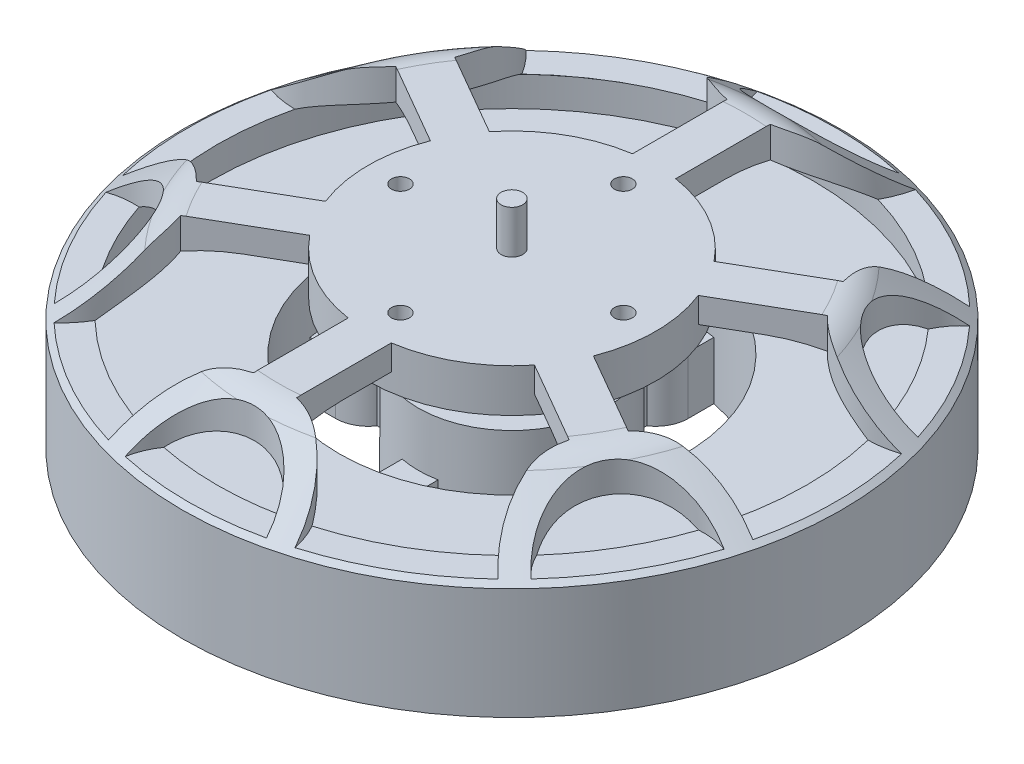
SolidWorks part; units mm, degrees
ref_plane "Front Plane" through (0, 0, 0) normal (0, 0, 1) x (1, 0, 0)
ref_plane "Top Plane" through (0, 0, 0) normal (0, 1, 0) x (1, 0, 0)
ref_plane "Right Plane" through (0, 0, 0) normal (1, 0, 0) x (0, 0, -1)
ref_axis "Axis1" through (0, 40.089, 0) along (0, -1, 0)
sketch "Sketch1" plane through (0, 0, 0) normal (0, 0, 1) x (1, 0, 0)
  line L0 (0, 0) -> (9.65, 0)
  line L1 (9.65, 0) -> (9.65, 3.93)
  line L2 (9.65, 3.93) -> (27.5, 3.93)
  line L3 (27.5, 3.93) -> (45.83, 8.08)
  line L4 (45.83, 8.08) -> (45.83, 23.58)
  line L5 (45.83, 23.58) -> (36.1322, 30.9557)
  line L6 (32.5, 32.18) -> (1.5, 32.18)
  line L7 (1.5, 32.18) -> (1.5, 38.18)
  line L8 (1.5, 38.18) -> (0, 38.18)
  line L9 (0, 38.18) -> (0, 0) construction
  line L10 (0, 0) -> (0, 38.18)
  arc A0 (36.1322, 30.9557) -> (32.5, 32.18) centre (32.5, 26.18) ccw
  dimension "D10" = 6
  dimension "D1" = 3
  dimension "D2" = 6
  dimension "D3" = 28.25
  dimension "D4" = 3.93
  dimension "D5" = 19.3
  dimension "D6" = 4.15
  dimension "D7" = 91.66
  dimension "D8" = 55
  dimension "D9" = 65
  dimension "D11" = 15.5
revolve "Revolve1" add sketch "Sketch1" angle 360 about L9
sketch "Sketch2" plane through (0, 3.93, 0) normal (0, -1, 0) x (1, 0, 0)
  line L0 (0, 0) -> (0, 27.5) construction
  line L1 (2.5, 12.7574) -> (2.5, 16.2583)
  line L2 (4.5, 20) -> (4.5, 23.5744)
  line L3 (0, 0) -> (16.9706, 16.9706) construction
  line L4 (20, 4.5) -> (23.5744, 4.5)
  line L5 (12.7574, 2.5) -> (16.2583, 2.5)
  line L6 (20, -4.5) -> (23.5744, -4.5)
  line L7 (4.5, -20) -> (4.5, -23.5744)
  line L8 (2.5, -12.7574) -> (2.5, -16.2583)
  line L9 (12.7574, -2.5) -> (16.2583, -2.5)
  line L10 (-4.5, -20) -> (-4.5, -23.5744)
  line L11 (-20, -4.5) -> (-23.5744, -4.5)
  line L12 (-12.7574, -2.5) -> (-16.2583, -2.5)
  line L13 (-2.5, -12.7574) -> (-2.5, -16.2583)
  line L14 (-20, 4.5) -> (-23.5744, 4.5)
  line L15 (-4.5, 20) -> (-4.5, 23.5744)
  line L16 (-2.5, 12.7574) -> (-2.5, 16.2583)
  line L17 (-12.7574, 2.5) -> (-16.2583, 2.5)
  arc A0 (4.5, 23.5744) -> (23.5744, 4.5) centre (0, 0) cw
  arc A1 (4.5, 20) -> (2.5, 16.2583) centre (0, 20) cw
  arc A2 (2.5, 12.7574) -> (12.7574, 2.5) centre (0, 0) cw
  circle A3 centre (0, 0) radius 27.5 construction
  arc A4 (20, 4.5) -> (16.2583, 2.5) centre (20, 0) ccw
  arc A5 (20, -4.5) -> (16.2583, -2.5) centre (20, 0) cw
  arc A6 (23.5744, -4.5) -> (4.5, -23.5744) centre (0, 0) cw
  arc A7 (4.5, -20) -> (2.5, -16.2583) centre (0, -20) ccw
  arc A8 (12.7574, -2.5) -> (2.5, -12.7574) centre (0, 0) cw
  arc A9 (-4.5, -20) -> (-2.5, -16.2583) centre (0, -20) cw
  arc A10 (-4.5, -23.5744) -> (-23.5744, -4.5) centre (0, 0) cw
  arc A11 (-20, -4.5) -> (-16.2583, -2.5) centre (-20, 0) ccw
  arc A12 (-2.5, -12.7574) -> (-12.7574, -2.5) centre (0, 0) cw
  arc A13 (-20, 4.5) -> (-16.2583, 2.5) centre (-20, 0) cw
  arc A14 (-23.5744, 4.5) -> (-4.5, 23.5744) centre (0, 0) cw
  arc A15 (-4.5, 20) -> (-2.5, 16.2583) centre (0, 20) ccw
  arc A16 (-12.7574, 2.5) -> (-2.5, 12.7574) centre (0, 0) cw
  point P4 (0, 20)
  point P51 (0, 0)
  dimension "D2" = 13
  dimension "D5" = 24
  dimension "D1" = 20
  dimension "D3" = 5
  dimension "D4" = 9
  dimension "D6" = 45
  dimension "D7" = 4
hole_wizard "M4x0.7 Tapped Hole1" positions "3DSketch1" profile "Sketch4" tap size "M4x0.7" standard "ANSI Metric"
sketch3d "3DSketch1"
  point P0 (-20, 3.93, 0)
  point P3 (0, 3.93, 20)
  point P6 (20, 3.93, 0)
  point P9 (0, 3.93, -20)
sketch "Sketch4" plane through (-20, 3.93, 0) normal (1, 0, 0) x (0, 0, -1)
  line L0 (0, 0) -> (0, 8.9914)
  line L1 (0, 8.9914) -> (1.65, 8)
  line L2 (1.65, 8) -> (1.65, 0)
  line L5 (1.65, 0) -> (0, 0)
  line L10 (0, 8.9914) -> (-1.65, 8) construction
  line L11 (0, -6.35) -> (0, 107.95) construction
  dimension "Tap Drill Dia." = 3.3
  dimension "Tap Drill Depth" = 8
  dimension "Drill Angle" = 118
cosmetic thread "Hole Thread1" parameters "D1"=7.874, "D2"=4
cosmetic thread "Hole Thread2" parameters "D1"=7.874, "D2"=4
cosmetic thread "Hole Thread3" parameters "D1"=7.874, "D2"=4
cosmetic thread "Hole Thread4" parameters "D1"=7.874, "D2"=4
extrude "Cut-Extrude1" cut sketch "Sketch2" against normal blind 8
sketch "Sketch5" plane through (0, 0, 0) normal (0, 0, 1) x (1, 0, 0)
  line L0 (24, 19.43) -> (41.83, 19.43)
  line L1 (-27.5, 3.93) -> (27.5, 3.93) construction
  line L2 (41.83, 19.43) -> (41.83, 23.58)
  line L3 (45.83, 8.08) -> (45.83, 23.58) construction
  line L4 (10, 19.43) -> (13, 19.43)
  line L5 (13, 19.43) -> (13, 11.93)
  line L6 (13, 11.93) -> (24, 11.93)
  line L7 (24, 11.93) -> (24, 19.43)
  line L8 (0, 40.089) -> (0, -1.909) construction
  line L9 (4.5, 11.93) -> (23.5744, 11.93) construction
  line L10 (45.83, 23.58) -> (-45.83, 23.58) construction
  line L11 (20, 28.68) -> (26.6996, 28.68)
  line L12 (32.5, 32.18) -> (-32.5, 32.18) construction
  line L13 (41.83, 23.58) -> (45.83, 20.5378) construction
  line L14 (45.83, 23.58) -> (36.1322, 30.9557) construction
  line L15 (20, 28.68) -> (20, 26.18)
  line L16 (20, 26.18) -> (10, 26.18)
  line L17 (10, 26.18) -> (10, 19.43)
  arc A0 (26.6996, 28.68) -> (41.83, 23.58) centre (26.6996, 3.6861) cw
  dimension "D1" = 15.5
  dimension "D2" = 4
  dimension "D3" = 13
  dimension "D4" = 24
  dimension "D5" = 3.5
  dimension "D6" = 20
  dimension "D7" = 6
  dimension "D8" = 10
revolve "Cut-Revolve3" cut sketch "Sketch5" angle 360 about axis through (0, 40.089, 0) along (0, -1, 0)
sketch "Sketch6" plane through (0, 0, 0) normal (0, 1, 0) x (1, 0, 0)
  line L0 (-3, 19.7737) -> (-3, 32.9241)
  line L1 (3, 19.7737) -> (3, 32.9241)
  line L2 (-3, 19.7737) -> (3, 19.7737) construction
  line L3 (0, 45.83) -> (0, 35.83) construction
  line L4 (15.6245, 12.4849) -> (27.0131, 19.0601)
  line L5 (18.6245, 7.2888) -> (30.0131, 13.864)
  line L6 (15.6245, 12.4849) -> (18.6245, 7.2888) construction
  line L7 (39.6899, 22.915) -> (31.0297, 17.915) construction
  line L8 (18.6245, -7.2888) -> (30.0131, -13.864)
  line L9 (15.6245, -12.4849) -> (27.0131, -19.0601)
  line L10 (18.6245, -7.2888) -> (15.6245, -12.4849) construction
  line L11 (39.6899, -22.915) -> (31.0297, -17.915) construction
  line L12 (3, -19.7737) -> (3, -32.9241)
  line L13 (-3, -19.7737) -> (-3, -32.9241)
  line L14 (3, -19.7737) -> (-3, -19.7737) construction
  line L15 (0, -45.83) -> (0, -35.83) construction
  line L16 (-15.6245, -12.4849) -> (-27.0131, -19.0601)
  line L17 (-18.6245, -7.2888) -> (-30.0131, -13.864)
  line L18 (-15.6245, -12.4849) -> (-18.6245, -7.2888) construction
  line L19 (-39.6899, -22.915) -> (-31.0297, -17.915) construction
  line L20 (-18.6245, 7.2888) -> (-30.0131, 13.864)
  line L21 (-15.6245, 12.4849) -> (-27.0131, 19.0601)
  line L22 (-18.6245, 7.2888) -> (-15.6245, 12.4849) construction
  line L23 (-39.6899, 22.915) -> (-31.0297, 17.915) construction
  line L24 (0, 15.5) -> (15.5, 0) construction
  line L25 (15.5, 0) -> (0, -15.5) construction
  line L26 (0, -15.5) -> (-15.5, 0) construction
  line L27 (-15.5, 0) -> (0, 15.5) construction
  arc A1 (-9.9403, 44.739) -> (9.9403, 44.739) centre (0, 45.83) ccw
  circle A2 centre (0, 0) radius 45.83 construction
  arc A3 (-13.1108, 43.9146) -> (-3, 32.9241) centre (0, 45.83) ccw
  arc A4 (13.1108, 43.9146) -> (3, 32.9241) centre (0, 45.83) cw
  arc A5 (-13.1108, 43.9146) -> (-9.9403, 44.739) centre (0, 0) cw
  arc A6 (9.9403, 44.739) -> (13.1108, 43.9146) centre (0, 0) cw
  arc A7 (33.775, 30.9781) -> (43.7153, 13.7609) centre (39.6899, 22.915) ccw
  arc A8 (31.4758, 33.3116) -> (27.0131, 19.0601) centre (39.6899, 22.915) ccw
  arc A9 (44.5866, 10.603) -> (30.0131, 13.864) centre (39.6899, 22.915) cw
  arc A10 (31.4758, 33.3116) -> (33.775, 30.9781) centre (0, 0) cw
  arc A11 (43.7153, 13.7609) -> (44.5866, 10.603) centre (0, 0) cw
  arc A12 (43.7153, -13.7609) -> (33.775, -30.9781) centre (39.6899, -22.915) ccw
  arc A13 (44.5866, -10.603) -> (30.0131, -13.864) centre (39.6899, -22.915) ccw
  arc A14 (31.4758, -33.3116) -> (27.0131, -19.0601) centre (39.6899, -22.915) cw
  arc A15 (44.5866, -10.603) -> (43.7153, -13.7609) centre (0, 0) cw
  arc A16 (33.775, -30.9781) -> (31.4758, -33.3116) centre (0, 0) cw
  arc A17 (9.9403, -44.739) -> (-9.9403, -44.739) centre (0, -45.83) ccw
  arc A18 (13.1108, -43.9146) -> (3, -32.9241) centre (0, -45.83) ccw
  arc A19 (-13.1108, -43.9146) -> (-3, -32.9241) centre (0, -45.83) cw
  arc A20 (13.1108, -43.9146) -> (9.9403, -44.739) centre (0, 0) cw
  arc A21 (-9.9403, -44.739) -> (-13.1108, -43.9146) centre (0, 0) cw
  arc A22 (-33.775, -30.9781) -> (-43.7153, -13.7609) centre (-39.6899, -22.915) ccw
  arc A23 (-31.4758, -33.3116) -> (-27.0131, -19.0601) centre (-39.6899, -22.915) ccw
  arc A24 (-44.5866, -10.603) -> (-30.0131, -13.864) centre (-39.6899, -22.915) cw
  arc A25 (-31.4758, -33.3116) -> (-33.775, -30.9781) centre (0, 0) cw
  arc A26 (-43.7153, -13.7609) -> (-44.5866, -10.603) centre (0, 0) cw
  arc A27 (-43.7153, 13.7609) -> (-33.775, 30.9781) centre (-39.6899, 22.915) ccw
  arc A28 (-44.5866, 10.603) -> (-30.0131, 13.864) centre (-39.6899, 22.915) ccw
  arc A29 (-31.4758, 33.3116) -> (-27.0131, 19.0601) centre (-39.6899, 22.915) cw
  arc A30 (-44.5866, 10.603) -> (-43.7153, 13.7609) centre (0, 0) cw
  arc A31 (-33.775, 30.9781) -> (-31.4758, 33.3116) centre (0, 0) cw
  arc A32 (3, 19.7737) -> (15.6245, 12.4849) centre (0, 0) cw
  arc A33 (18.6245, 7.2888) -> (18.6245, -7.2888) centre (0, 0) cw
  arc A34 (15.6245, -12.4849) -> (3, -19.7737) centre (0, 0) cw
  arc A35 (-3, -19.7737) -> (-15.6245, -12.4849) centre (0, 0) cw
  arc A36 (-18.6245, -7.2888) -> (-18.6245, 7.2888) centre (0, 0) cw
  arc A37 (-3, 19.7737) -> (-15.6245, 12.4849) centre (0, 0) ccw
  point P0 (0, 19.7737)
  point P17 (0, 15.5)
  point P28 (15.5, 0)
  point P38 (0, -15.5)
  point P68 (0, 0)
  point P69 (-15.5, 0)
  dimension "D1" = 6
  dimension "D3" = 3.25
  dimension "D5" = 20
  dimension "D2" = 6
  dimension "D4" = 10
  dimension "D6" = 15.5
extrude "Cut-Extrude3" cut sketch "Sketch6" against normal blind 8 from surface at 32.18 flip side to cut starting at face at (0, 32.18, 1.5)
hole_wizard "M3x0.5 Tapped Hole1" positions "Sketch8" profile "Sketch10" tap size "M3x0.5" standard "ANSI Metric" end condition up to next
sketch "Sketch8" plane through (0, 32.18, 0) normal (0, 1, 0) x (1, 0, 0)
  point P0 (0, 15.5)
  point P3 (15.5, 0)
  point P6 (0, -15.5)
  point P9 (-15.5, 0)
sketch "Sketch10" plane through (0, 32.18, -15.5) normal (1, 0, 0) x (0, 0, 1)
  line L0 (0, 0) -> (0, 6)
  line L1 (0, 6) -> (1.25, 6)
  line L2 (1.25, 6) -> (1.25, 0)
  line L5 (1.25, 0) -> (0, 0)
  line L11 (0, -6.35) -> (0, 107.95) construction
  dimension "Thru Tap Drill Dia." = 2.5
  dimension "Thru Tap Drill Depth" = 6
cosmetic thread "Hole Thread5" parameters "D2"=3
cosmetic thread "Hole Thread6" parameters "D2"=3
cosmetic thread "Hole Thread7" parameters "D2"=3
cosmetic thread "Hole Thread8" parameters "D2"=3
sketch "Sketch11" plane through (0, 0, 0) normal (0, 1, 0) x (1, 0, 0)
  line L0 (-26.0427, 21.4465) -> (-21.4465, 26.0427) construction
  line L1 (-27.9873, 23.3911) -> (-23.3911, 27.9873)
  line L2 (-24.0982, 19.502) -> (-19.502, 24.0982)
  line L3 (-23.7446, 23.7446) -> (0, 0) construction
  line L4 (-20, 0) -> (0, 20) construction
  line L5 (-27.9873, 19.502) -> (-19.502, 27.9873) construction
  line L6 (-25.6892, 25.6892) -> (-32.4067, 32.4067) construction
  arc A0 (-27.9873, 23.3911) -> (-24.0982, 19.502) centre (-26.0427, 21.4465) ccw
  arc A1 (-19.502, 24.0982) -> (-23.3911, 27.9873) centre (-21.4465, 26.0427) ccw
  arc A2 (3, 19.7737) -> (-3, 19.7737) centre (0, 0) ccw construction
  circle A3 centre (0, 0) radius 45.83 construction
  point P2 (-23.7446, 23.7446)
  dimension "D1" = 12
  dimension "D2" = 5.5
  dimension "D3" = 9.5
extrude "Boss-Extrude1" add sketch "Sketch11" against normal blind 19.05 from offset 12.7
equation "\"INTERIOR_STATOR_BORE_OD\"= 48MM"
equation "\"INTERIOR_STATOR_BORE_ID\"= 26mm"
equation "\"D5@Sketch2\"=\"INTERIOR_STATOR_BORE_OD\"/2"
equation "\"D2@Sketch2\"=\"INTERIOR_STATOR_BORE_ID\"/2"
equation "\"D3@Sketch5\"=\"INTERIOR_STATOR_BORE_ID\"/2"
equation "\"D4@Sketch5\"=\"INTERIOR_STATOR_BORE_OD\"/2"
